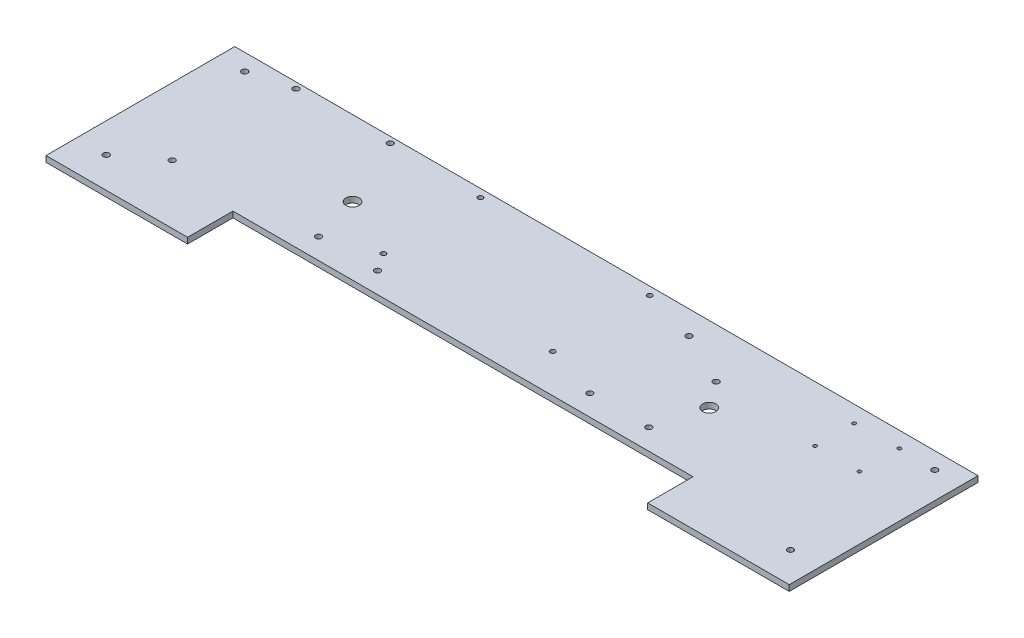
SolidWorks part; units mm, degrees
ref_plane "Front Plane" through (0, 0, 0) normal (0, 0, 1) x (1, 0, 0)
ref_plane "Top Plane" through (0, 0, 0) normal (0, 1, 0) x (1, 0, 0)
ref_plane "Right Plane" through (0, 0, 0) normal (1, 0, 0) x (0, 0, -1)
sketch "Sketch1" plane through (0, 0, 0) normal (0, 1, 0) x (1, 0, 0)
  line L0 (0, 0) -> (495.3, 0)
  line L1 (495.3, 0) -> (495.3, -48.8188)
  line L2 (495.3, -48.8188) -> (647.7, -48.8188)
  line L3 (647.7, -48.8188) -> (647.7, 154.3812)
  line L4 (647.7, 154.3812) -> (-152.4, 154.3812)
  line L5 (0, 0) -> (0, -48.8188)
  line L6 (0, -48.8188) -> (-152.4, -48.8188)
  line L7 (-152.4, -48.8188) -> (-152.4, 154.3812)
  dimension "D1" = 203.2
  dimension "D2" = 203.2
  dimension "D3" = 495.3
  dimension "D4" = 800.1
  dimension "D5" = 152.4
  dimension "D6" = 152.4
  dimension "D7" = 154.3812
extrude "Boss-Extrude1" add sketch "Sketch1" along normal blind 6.35 contours L4 L7 L6 L5 L0 L1 L2 L3
sketch "Sketch3" plane through (0, 6.35, 0) normal (0, 1, 0) x (1, 0, 0)
  line L0 (-152.4, -48.8188) -> (-152.4, 154.3812) construction
  line L1 (0, -48.8188) -> (-152.4, -48.8188) construction
  line L3 (647.7, 154.3812) -> (-152.4, 154.3812) construction
  line L5 (0, 0) -> (495.3, 0) construction
  line L8 (647.7, -48.8188) -> (647.7, 154.3812) construction
  line L9 (495.3, -48.8188) -> (647.7, -48.8188) construction
  circle A0 centre (-120.65, -15.7988) radius 3.302
  circle A1 centre (-80.0608, 14.6304) radius 3.175
  circle A2 centre (-123.825, 136.4183) radius 3.302
  circle A3 centre (-80.0608, 147.9804) radius 3.175
  circle A4 centre (21.463, 147.9804) radius 3.175
  circle A5 centre (55.626, 73.1012) radius 7.1438
  circle A6 centre (619.125, 136.4183) radius 3.175
  circle A7 centre (615.95, -15.7988) radius 3.175
  circle A8 centre (580.009, 137.4648) radius 1.905
  circle A9 centre (532.257, 94.4118) radius 1.905
  circle A10 centre (580.009, 94.4118) radius 1.905
  circle A11 centre (532.257, 136.4183) radius 1.905
  circle A12 centre (439.674, 73.1012) radius 7.1438
  dimension "D1" = 6.604
  dimension "D2" = 31.75
  dimension "D3" = 33.02
  dimension "D4" = 6.35
  dimension "D5" = 72.3392
  dimension "D6" = 63.4492
  dimension "D7" = 6.604
  dimension "D8" = 28.575
  dimension "D9" = 17.9629
  dimension "D10" = 6.35
  dimension "D11" = 6.4008
  dimension "D12" = 72.3392
  dimension "D13" = 6.35
  dimension "D14" = 173.863
  dimension "D15" = 6.4008
  dimension "D16" = 14.2875
  dimension "D17" = 208.026
  dimension "D18" = 73.1012
  dimension "D20" = 6.35
  dimension "D21" = 28.575
  dimension "D22" = 17.9629
  dimension "D23" = 6.35
  dimension "D24" = 31.75
  dimension "D25" = 33.02
  dimension "D26" = 3.81
  dimension "D27" = 67.691
  dimension "D28" = 16.9164
  dimension "D29" = 3.81
  dimension "D30" = 59.9694
  dimension "D31" = 115.443
  dimension "D32" = 3.81
  dimension "D33" = 67.691
  dimension "D34" = 59.9694
  dimension "D35" = 3.81
  dimension "D36" = 17.9629
  dimension "D37" = 115.443
  dimension "D38" = 14.2875
  dimension "D39" = 81.28
  dimension "D40" = 208.026
extrude "Cut-Extrude1" cut sketch "Sketch3" against normal blind 7.62
sketch "Sketch5" plane through (0, 6.35, 0) normal (0, 1, 0) x (1, 0, 0)
  line L0 (647.7, 154.3812) -> (-152.4, 154.3812) construction
  line L1 (63.5, 154.3812) -> (431.8, 154.3812)
  line L2 (63.5, 154.3812) -> (63.5, 0)
  line L3 (63.5, 0) -> (431.8, 0)
  line L4 (431.8, 154.3812) -> (431.8, 0)
  line L5 (0, 0) -> (495.3, 0) construction
  line L8 (-152.4, -48.8188) -> (-152.4, 154.3812) construction
  line L9 (0, 0) -> (0, -48.8188) construction
  circle A0 centre (120.65, 145.7452) radius 2.667
  circle A1 centre (55.626, 73.1012) radius 7.1438 construction
  circle A2 centre (120.65, 41.3512) radius 2.667
  circle A3 centre (439.674, 73.1012) radius 7.1438 construction
  circle A4 centre (419.1, 101.0412) radius 3.175
  circle A5 centre (425.45, 22.3012) radius 3.175
  circle A6 centre (361.95, 128.9812) radius 3.175
  circle A7 centre (361.95, 22.3012) radius 3.175
  circle A8 centre (302.9204, 145.7452) radius 2.667
  circle A9 centre (302.9204, 41.3512) radius 2.667
  circle A10 centre (133.35, 22.3012) radius 3.175
  circle A11 centre (69.85, 22.3012) radius 3.175
  circle A12 centre (21.463, 147.9804) radius 3.175 construction
  dimension "D5" = 7.874
  dimension "D7" = 63.5
  dimension "D1" = 7.874
  dimension "D9" = 6.35
  dimension "D10" = 12.7
  dimension "D11" = 53.34
  dimension "D12" = 6.35
  dimension "D13" = 6.35
  dimension "D14" = 22.3012
  dimension "D15" = 6.35
  dimension "D16" = 25.4
  dimension "D17" = 69.85
  dimension "D18" = 6.35
  dimension "D19" = 22.3012
  dimension "D20" = 69.85
  dimension "D21" = 5.334
  dimension "D22" = 8.636
  dimension "D23" = 128.8796
  dimension "D24" = 5.334
  dimension "D25" = 128.8796
  dimension "D26" = 113.03
  dimension "D27" = 5.334
  dimension "D28" = 8.636
  dimension "D29" = 311.15
  dimension "D30" = 5.334
  dimension "D31" = 113.03
  dimension "D32" = 311.15
  dimension "D33" = 6.35
  dimension "D34" = 22.3012
  dimension "D35" = 298.45
  dimension "D36" = 6.35
  dimension "D37" = 22.3012
  dimension "D38" = 6.35
  dimension "D39" = 42.037
  dimension "D2" = 7.874
  dimension "D3" = 215.9
  dimension "D4" = 7.874
  dimension "D6" = 368.3
  dimension "D8" = 154.3812
extrude "Cut-Extrude2" cut sketch "Sketch5" against normal blind 7.62 contours A11 | A2 | A10 | A0 | A8 | A6 | A9 | A4 | A7 | A5
